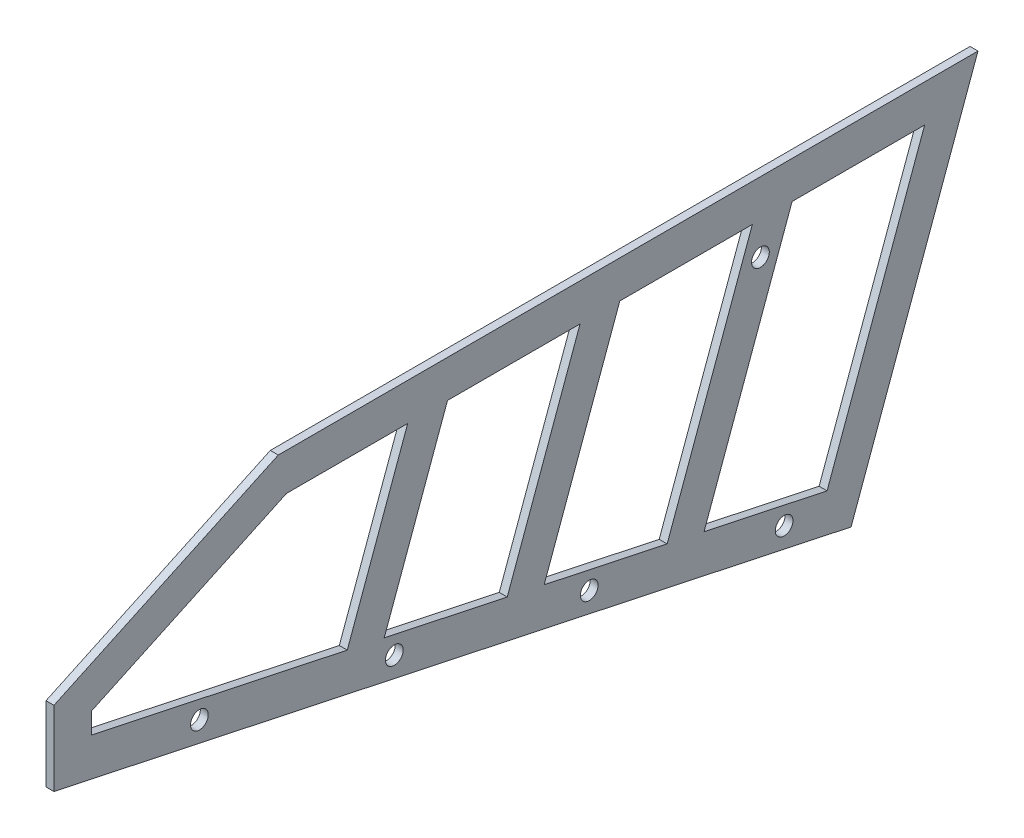
SolidWorks part; units mm, degrees
ref_plane "Front Plane" through (0, 0, 0) normal (0, 0, 1) x (1, 0, 0)
ref_plane "Top Plane" through (0, 0, 0) normal (0, 1, 0) x (1, 0, 0)
ref_plane "Right Plane" through (0, 0, 0) normal (1, 0, 0) x (0, 0, -1)
sketch "Sketch1" plane through (0, 0, 0) normal (1, 0, 0) x (0, 0, -1)
  line L0 (16.1785, 44.45) -> (0, 0)
  line L1 (0, 0) -> (-101.6, 21.5957)
  line L2 (-101.6, 21.5957) -> (-101.6, 31.1207)
  line L3 (-101.6, 31.1207) -> (-73.0153, 44.45)
  line L4 (-73.0153, 44.45) -> (16.1785, 44.45)
  line L5 (0, 0) -> (32.2993, 0) construction
  dimension "D1" = 9.525
  dimension "D2" = 44.45
  dimension "D3" = 101.6
  dimension "D4" = 70
  dimension "D5" = 12
  dimension "D6" = 65
extrude "Extrude1" add sketch "Sketch1" along normal blind 0.635
sketch "Sketch2" plane through (0, 0, 0) normal (-1, 0, 0) x (0, 0, 1)
  line L0 (-0.8773, 2.4103) -> (101.6, 24.1925) construction
  line L1 (0, 0) -> (-16.1785, 44.45) construction
  line L2 (101.6, 31.1207) -> (101.6, 21.5957) construction
  line L3 (101.6, 21.5957) -> (0, 0) construction
  circle A0 centre (8.5311, 4.4101) radius 1.5875
  circle A1 centre (33.3761, 9.6911) radius 1.5875
  circle A2 centre (58.221, 14.972) radius 1.5875
  circle A3 centre (83.066, 20.253) radius 1.5875
  dimension "D2" = 25.4
  dimension "D3" = 25.4
  dimension "D4" = 25.4
  dimension "D5" = 9.525
  dimension "D6" = 3.175
  dimension "D1" = 2.54
extrude "Extrude2" cut sketch "Sketch2" against normal through all
sketch "Sketch3" plane through (0.635, 0, 0) normal (-1, 0, 0) x (0, 0, 1)
  line L0 (-16.1785, 44.45) -> (0, 0)
  line L1 (0, 0) -> (101.6, 21.5957)
  line L2 (101.6, 21.5957) -> (101.6, 31.1207)
  line L3 (-16.1785, 44.45) -> (73.0153, 44.45)
  line L4 (73.0153, 44.45) -> (101.6, 31.1207)
  line L5 (7.5169, 39.6875) -> (-9.3769, 39.6875)
  line L6 (23.4442, 9.8521) -> (39.1249, 13.1852)
  line L7 (29.4789, 39.6875) -> (39.1249, 13.1852)
  line L8 (34.547, 39.6875) -> (43.8291, 14.1851)
  line L9 (29.4789, 39.6875) -> (12.585, 39.6875)
  line L10 (7.5169, 39.6875) -> (18.74, 8.8522)
  line L11 (12.585, 39.6875) -> (23.4442, 9.8521)
  line L12 (43.8291, 14.1851) -> (59.5098, 17.5181)
  line L13 (51.4408, 39.6875) -> (59.5098, 17.5181)
  line L14 (56.509, 39.6875) -> (64.214, 18.518)
  line L15 (71.9595, 39.6875) -> (-9.3769, 39.6875)
  line L16 (-9.3769, 39.6875) -> (3.0593, 5.5192)
  line L17 (3.0593, 5.5192) -> (96.8375, 25.4523)
  line L18 (96.8375, 25.4523) -> (96.8375, 28.0867)
  line L19 (96.8375, 28.0867) -> (71.9595, 39.6875)
  line L20 (71.9595, 39.6875) -> (56.509, 39.6875)
  line L21 (-9.3769, 39.6875) -> (3.0593, 5.5192)
  line L22 (3.0593, 5.5192) -> (18.74, 8.8522)
  line L23 (96.8375, 25.4523) -> (96.8375, 28.0867)
  line L24 (96.8375, 28.0867) -> (71.9595, 39.6875)
  line L25 (51.4408, 39.6875) -> (34.547, 39.6875)
  line L26 (64.214, 18.518) -> (96.8375, 25.4523)
  circle A0 centre (8.5311, 4.4101) radius 1.1303
  circle A1 centre (33.3761, 9.6911) radius 1.1303
  circle A2 centre (58.221, 14.972) radius 1.1303
  circle A3 centre (83.066, 20.253) radius 1.1303
  dimension "D2" = 2.2606
  dimension "D3" = 4.7625
  dimension "D4" = 15.875
  dimension "D5" = 4.7625
  dimension "D6" = 15.875
  dimension "D7" = 15.875
  dimension "D8" = 4.7625
  dimension "D1" = 4.7625
extrude "Extrude3" add sketch "Sketch3" against normal blind 1.016 separate body
sketch "Sketch4" plane through (0, 0, 0) normal (-1, 0, 0) x (0, 0, 1)
  line L10 (73.0153, 44.45) -> (-16.1785, 44.45)
  line L11 (-16.1785, 44.45) -> (0, 0)
  line L12 (0, 0) -> (101.6, 21.5957)
  line L13 (101.6, 21.5957) -> (101.6, 31.1207)
  line L14 (101.6, 31.1207) -> (73.0153, 44.45)
  line L15 (73.0153, 44.45) -> (-16.1785, 44.45)
  line L16 (-16.1785, 44.45) -> (0, 0)
  line L17 (0, 0) -> (101.6, 21.5957)
  line L18 (101.6, 21.5957) -> (101.6, 31.1207)
  line L19 (101.6, 31.1207) -> (73.0153, 44.45)
  dimension "D1" = 0
extrude "Extrude4" cut sketch "Sketch4" against normal up to next (0.635 mm away)
sketch "Sketch5" plane through (1.651, 0, 0) normal (1, 0, 0) x (0, 0, -1)
  line L0 (-8.3176, 44.45) -> (-22.737, 4.8329) construction
  line L1 (-73.0153, 44.45) -> (16.1785, 44.45) construction
  line L2 (0, 0) -> (-101.6, 21.5957) construction
  line L3 (-12.585, 39.6875) -> (-23.4442, 9.8521) construction
  circle A0 centre (-11.5533, 35.56) radius 1.1303
  circle A1 centre (-8.5311, 4.4101) radius 1.1303 construction
  dimension "D2" = 8.89
  dimension "D1" = 2.3813
extrude "Cut-Extrude1" cut sketch "Sketch5" against normal through all
